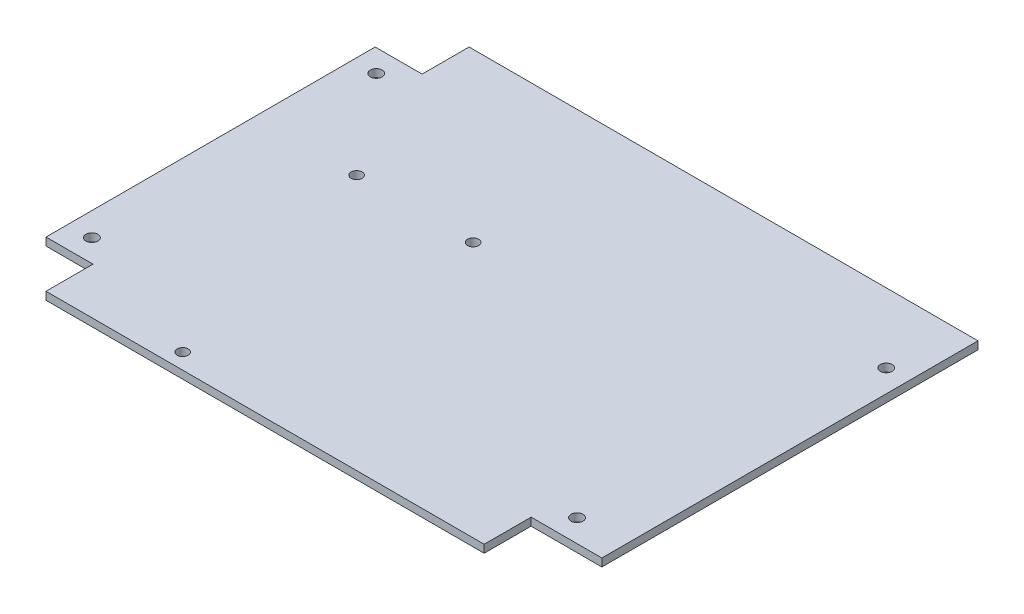
SolidWorks part; units mm, degrees
ref_plane "Front Plane" through (0, 0, 0) normal (0, 0, 1) x (1, 0, 0)
ref_plane "Top Plane" through (0, 0, 0) normal (0, 1, 0) x (1, 0, 0)
ref_plane "Right Plane" through (0, 0, 0) normal (1, 0, 0) x (0, 0, -1)
sketch "Sketch1" plane through (0, 0, 0) normal (0, 1, 0) x (1, 0, 0)
  line L1 (112.7633, -85.8266) -> (-112.7633, -85.8266)
  line L2 (112.7633, -85.8266) -> (112.7633, 85.8266)
  line L3 (112.7633, 85.8266) -> (-112.7633, 85.8266)
  line L4 (-112.7633, -85.8266) -> (-112.7633, 85.8266)
  line L5 (112.7633, -85.8266) -> (-112.7633, 85.8266) construction
  line L6 (112.7633, 85.8266) -> (-112.7633, -85.8266) construction
  point P0 (0, 0)
  dimension "D2" = 171.6532
  dimension "D1" = 225.5266
extrude "Boss-Extrude1" add sketch "Sketch1" along normal blind 3.175
sketch "Sketch2" plane through (0, 3.175, 0) normal (0, 1, 0) x (1, 0, 0)
  line L0 (-112.7633, 85.8266) -> (-112.7633, -85.8266) construction
  line L1 (-112.7633, 85.8266) -> (-93.7133, 85.8266)
  line L2 (-112.7633, 85.8266) -> (-112.7633, 66.7766)
  line L3 (-112.7633, 66.7766) -> (-93.7133, 66.7766)
  line L4 (-93.7133, 85.8266) -> (-93.7133, 66.7766)
  line L9 (112.7633, -85.8266) -> (84.0613, -85.8266)
  line L10 (112.7633, -85.8266) -> (112.7633, -66.7766)
  line L11 (112.7633, -66.7766) -> (84.0613, -66.7766)
  line L12 (84.0613, -85.8266) -> (84.0613, -66.7766)
  line L13 (-112.7633, -85.8266) -> (-93.7133, -85.8266)
  line L14 (-112.7633, -85.8266) -> (-112.7633, -66.7766)
  line L15 (-112.7633, -66.7766) -> (-93.7133, -66.7766)
  line L16 (-93.7133, -85.8266) -> (-93.7133, -66.7766)
  line L17 (-112.7633, -85.8266) -> (112.7633, -85.8266) construction
  dimension "D1" = 19.05
  dimension "D2" = 177.7746
extrude "CornerCut" cut sketch "Sketch2" against normal through all
sketch "Sketch3" plane through (0, 3.175, 0) normal (0, 1, 0) x (1, 0, 0)
  line L0 (-103.2383, 66.7766) -> (-103.2383, 57.6834) construction
  line L1 (-112.7633, 66.7766) -> (-93.7133, 66.7766) construction
  line L2 (-103.2383, -66.7766) -> (-103.2383, -57.6834) construction
  line L3 (-93.7133, -66.7766) -> (-112.7633, -66.7766) construction
  line L4 (93.5863, -66.7766) -> (93.5863, -57.6834) construction
  line L6 (103.6701, 66.7766) -> (103.6701, 57.6834) construction
  line L7 (84.0613, -66.7766) -> (84.0613, -85.8266) construction
  line L8 (-93.7133, 66.7766) -> (112.7633, 66.7766) construction
  line L9 (112.7633, -66.7766) -> (112.7633, 85.8266) construction
  line L10 (112.7633, -66.7766) -> (84.0613, -66.7766) construction
  circle A0 centre (-103.2383, 57.6834) radius 2.4257
  circle A1 centre (-103.2383, -57.6834) radius 2.4257
  circle A2 centre (93.5863, -57.6834) radius 2.4257
  circle A3 centre (103.6701, 57.6834) radius 2.4257
  point P14 (0, 0)
  point P15 (-103.2383, -57.6834)
  dimension "D2" = 4.8514
  dimension "D1" = 9.0932
  dimension "D3" = 9.525
  dimension "D4" = 9.0932
extrude "MountHoles" cut sketch "Sketch3" against normal through all
hole_wizard "#8 Clearance Hole1" positions "Sketch4" profile "Sketch5" hole size "#8" standard "ANSI Inch" end condition through all
sketch "Sketch4" plane through (0, 3.175, 0) normal (0, 1, 0) x (1, 0, 0)
  line L0 (-93.7133, -85.8266) -> (84.0613, -85.8266) construction
  line L1 (-112.7633, 66.7766) -> (-112.7633, -66.7766) construction
  point P0 (-44.6298, -79.4766)
  point P2 (-24.2443, 17.9822)
  point P4 (-71.4883, 17.9822)
  dimension "D1" = 99.568
  dimension "D2" = 101.092
  dimension "D3" = 47.244
  dimension "D4" = 6.35
  dimension "D5" = 41.275
sketch "Sketch5" plane through (-44.6298, 3.175, 79.4766) normal (1, 0, 0) x (0, 0, 1)
  line L0 (0, 0) -> (0, 3.175)
  line L1 (0, 3.175) -> (2.2479, 3.175)
  line L2 (2.2479, 3.175) -> (2.2479, 0)
  line L5 (2.2479, 0) -> (0, 0)
  line L11 (0, -6.35) -> (0, 107.95) construction
  dimension "Thru Hole Dia." = 4.4958
  dimension "Thru Hole Depth" = 3.175
equation "\"Height\"= 32in"
equation "\"Width\"= 23in"
equation "\"Depth\"= 20in"
equation "\"Plexi\"= .121in"
equation "\"MagnetThickness\"= 0.125in"
equation "\"MagnetDiameter\"= 12mm"
equation "\"DoorPlexi\" = \"Plexi\""
equation "\"BasePlateThickness\" = 0.5in"
equation "\"BasePlateWidth\" = \"Width\"+\"EBWidth\"-2*\"Plexi\""
equation "\"BasePlateDepth\" = \"TopBarDepth\"+2*\"CornerCube\""
equation "\"Boxsize\" = .75in"
equation "\"BoxsizeHalf\" = \"Boxsize\"/2"
equation "\"Boxinner\" = .625in"
equation "\"CornerCube\" = 0.75in"
equation "\"FingerLength\" = 1.125in"
equation "\"FingerWidth\" = .625in"
equation "\"Cutwidth\"= .016in"
equation "\"Earsize\"= 1in + \"Cutwidth\" /2"
equation "\"Slotsize\" = 1in - \"CutWidth\" / 2"
equation "\"InnerWidth\" = \"Width\" - 2* \"Plexi\""
equation "\"InnerHeight\" = \"Height\" -2 * \"Plexi\""
equation "\"InnerDepth\" = \"Depth\" - 2*\"Plexi\""
equation "\"RearNumHoles\" = 4"
equation "\"RearHolesBorder\" = 2.25"
equation "\"RearHoleSpacing\" = (\"Width\" - 2*\"RearHolesBorder\") / (\"RearNumHoles\"-1)"
equation "\"RearBarLength\" = (\"InnerWidth\"-2*\"CornerCube\")"
equation "\"RearTopNumHoles\" = 4"
equation "\"RearTopHolesBorder\" = 3.1"
equation "\"RearTopHolesSpacing\" = (\"Width\" - 2*\"RearTopHolesBorder\") / (\"RearTopNumHoles\"-1)"
equation "\"SideTopNumHoles\" = 4"
equation "\"SideTopHoleOffset\"=\"CornerCube\"+\"FingerLength\"+\"Plexi\"+.5"
equation "\"SideHorizNumHoles\" = 4"
equation "\"SideHorizHoleBorder\" = 1.50"
equation "\"SideVertBarLength\"=\"Height\"-\"BasePlateThickness\"-2*\"CornerCube\"-\"Plexi\""
equation "\"SideVertNumHoles\" = 4"
equation "\"SideVertHolesBorder\" = \"CornerCube\"+\"FingerLength\"+1.50"
equation "\"SideVertHoleSpacing\" = (\"InnerHeight\" - 2*\"SideVertHolesBorder\") / (\"SideVertNumHoles\"-1)"
equation "\"RearSideVertNumHoles\" = 4"
equation "\"RearSideVertHolesBorder\" = 2.4"
equation "\"RearSideVertHoleSpacing\" = (\"InnerHeight\" - 2*\"RearSideVertHolesBorder\") / (\"RearSideVertNumHoles\"-1)"
equation "\"RivetDia\" = .228in"
equation "\"SlotDepth\" = \"Plexi\" + 0.75in + .005in"
equation "\"SideSlotWidth\"   = \"Plexi\"+.005in"
equation "\"SidePanelVertSpacing\" = (\"Height\"-2*(1.75-\"Plexi\")) / 5"
equation "\"BottomPanelSideHoleSpacing\" = (\"InnerDepth\"-2*(1.75-\"Plexi\")) / 4"
equation "\"FrontDoorGap\" = .1in"
equation "\"TopDepth\" = \"Depth\"-\"DoorPlexi\"-\"FrontDoorGap\""
equation "\"TopBarDepth\" = \"Depth\"-\"DoorPlexi\"-\"Plexi\"-2*\"MagnetThickness\"-2*\"CornerCube\""
equation "\"CoolerDepth\" = 12in"
equation "\"ShelfDepth\" = \"TopBarDepth\"+\"CornerCube\"-\"CoolerDepth\""
equation "\"ShelfBarWidth\" = \"EBWidth\"-\"Boxsize\""
equation "\"ShelfGap\" = 0.5in"
equation "\"ShelfBarWidthShort\" = \"ShelfBarWidth\"-\"Boxsize\"-\"ShelfGap\""
equation "\"IntakeWidth\"=4in"
equation "\"IntakeHeight\"=2in"
equation "\"ExhaustWidth\"=4in"
equation "\"ExhaustHeight\"=2in"
equation "\"VentSpacing\"=7in"
equation "\"AngleBracketLength\"=20mm"
equation "\"AngleBracketWidth\"=.5in"
equation "\"AngleBracketThickness\"=.125in"
equation "\"AngleBracketHolePos\"=15mm"
equation "\"AngleBracketHoleDia\"=\"Rivet3_16Dia\""
equation "\"ShelfBarAngleHole\"=\"ShelfGap\"+\"Boxsize\"+\"AngleBracketHolePosShort\""
equation "\"SideTopHoleSpacing\" = (\"TopBarDepth\"-2*\"SideTopHoleOffset\") / (\"SideTopNumHoles\"-1)"
equation "\"SideHorizHoleSpacing\" = (\"TopBarDepth\"-2*\"SideHorizHoleBorder\") / (\"SideHorizNumHoles\"-1)"
equation "\"ShelfWidth\" = \"EBWidth\"-\"ShelfGap\""
equation "\"D2@Sketch1\"=\"ShelfDepth\""
equation "\"D1@Boss-Extrude1\"=\"ShelfThickness\""
equation "\"D1@Sketch2\"=\"Boxsize\""
equation "\"D1@Sketch3\"=\"AngleBracketHolePosShort\""
equation "\"D2@Sketch3\"=\"Rivet3_16Dia\""
equation "\"EBWidth\" = 9in"
equation "\"ShelfBarDepth\"=\"ShelfDepth\"-2*\"CornerCube\""
equation "\"ComponentMountDia\"=0.1770"
equation "\"ShelfThickness\" = .1250in"
equation "\"ShelfHeight1\" = 13in"
equation "\"ShelfHeight2\" = 24in"
equation "\"VentVertLocation\"=12.75in"
equation "\"Rivet3_16Dia\" = .191in"
equation "\"BinderPostDia\" = .228in"
equation "\"PSBracketThickness\" = .0641in"
equation "\"EBForwardMountOffset\" = 4.0in"
equation "\"EBForwardMount\" = 2*\"Boxsize\"+\"CoolerDepth\"+\"EBForwardMountOffset\""
equation "\"EBRearwardMountOffset\" = 1.5in"
equation "\"EBRearwardMount\"= \"Boxsize\"+\"EBRearwardMountOffset\""
equation "\"AngleBracketLengthShort\"=.625in"
equation "\"AngleBracketLengthLong\"=1in"
equation "\"AngleBracketHolePosShort\"=.358in"
equation "\"AngleBracketHolePosLong\"=.7in"
equation "\"D4@Sketch3\"=\"AngleBracketHolePosShort\""
equation "\"D3@Sketch3\"=\"BoxsizeHalf\""
